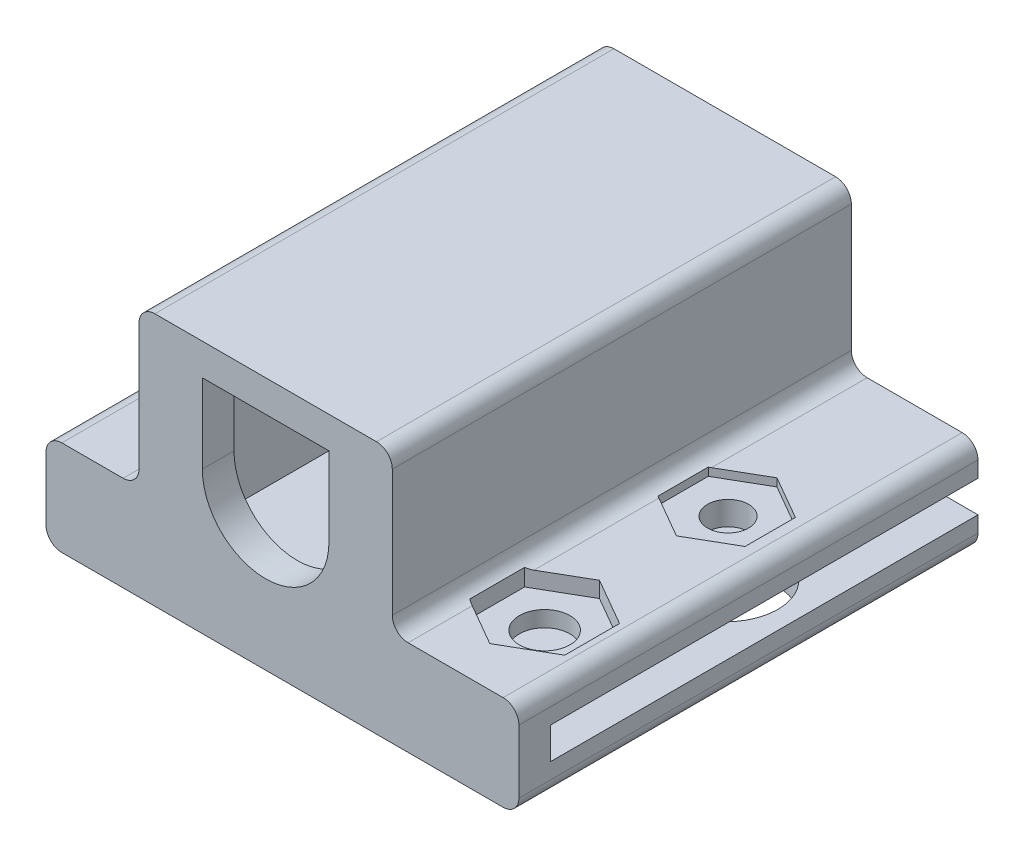
SolidWorks part; units mm, degrees
ref_plane "前视基准面" through (0, 0, 0) normal (0, 0, 1) x (1, 0, 0)
ref_plane "上视基准面" through (0, 0, 0) normal (0, 1, 0) x (1, 0, 0)
ref_plane "右视基准面" through (0, 0, 0) normal (1, 0, 0) x (0, 0, -1)
sketch "草图1" plane through (0, 0, 0) normal (0, 0, 1) x (1, 0, 0)
  line L1 (-12.875, -3) -> (-9, -3)
  line L2 (-13.875, -4) -> (-13.875, -8)
  line L3 (-12.875, -9) -> (15, -9)
  line L4 (5.5, 5) -> (-5.5, 5)
  line L5 (-6, 4.5) -> (-6, -4.5)
  line L6 (-5.5, -5) -> (5.5, -5)
  line L7 (6, -4.5) -> (6, 4.5)
  line L8 (5.5, 5) -> (-5.5, 5)
  line L9 (-6, 4.5) -> (-6, -4.5)
  line L10 (-5.5, -5) -> (5.5, -5)
  line L11 (6, -4.5) -> (6, 4.5)
  line L12 (-11.875, -7) -> (88.125, -7)
  line L13 (88.125, -7) -> (88.125, -5)
  line L14 (88.125, -5) -> (-11.875, -5)
  line L15 (-11.875, -5) -> (-11.875, -7)
  line L16 (-11.875, -7) -> (88.125, -7)
  line L17 (88.125, -7) -> (88.125, -5)
  line L18 (88.125, -5) -> (-11.875, -5)
  line L19 (-11.875, -5) -> (-11.875, -7)
  line L20 (16, -4) -> (16, -8)
  line L21 (-7, 7) -> (7, 7)
  line L22 (-8, 6) -> (-8, -2)
  line L23 (-8, -5) -> (8, -5)
  line L24 (8, 6) -> (8, -2)
  line L25 (9, -3) -> (15, -3)
  line L27 (0.8292, -1.25) -> (0.8292, 1.25)
  line L28 (0.8292, -1.25) -> (0.8292, 1.25)
  line L30 (-4, 0) -> (-4, 5)
  line L31 (-4, 5) -> (4, 5)
  line L32 (4, 0) -> (4, 5)
  arc A0 (-4, 0) -> (4, 0) centre (0, 0) ccw
  arc A1 (0.8292, 1.25) -> (0.8292, -1.25) centre (0, 0) ccw
  arc A2 (0.8292, 1.25) -> (0.8292, -1.25) centre (0, 0) ccw
  arc A3 (-7, 7) -> (-8, 6) centre (-7, 6) ccw
  arc A4 (6, 4.5) -> (5.5, 5) centre (5.5, 4.5) ccw
  arc A5 (-5.5, 5) -> (-6, 4.5) centre (-5.5, 4.5) ccw
  arc A6 (-6, -4.5) -> (-5.5, -5) centre (-5.5, -4.5) ccw
  arc A7 (5.5, -5) -> (6, -4.5) centre (5.5, -4.5) ccw
  arc A8 (6, 4.5) -> (5.5, 5) centre (5.5, 4.5) ccw
  arc A9 (-5.5, 5) -> (-6, 4.5) centre (-5.5, 4.5) ccw
  arc A10 (-6, -4.5) -> (-5.5, -5) centre (-5.5, -4.5) ccw
  arc A11 (5.5, -5) -> (6, -4.5) centre (5.5, -4.5) ccw
  arc A12 (-9, -3) -> (-8, -2) centre (-9, -2) ccw
  arc A13 (-12.875, -3) -> (-13.875, -4) centre (-12.875, -4) ccw
  arc A14 (-12.875, -9) -> (-13.875, -8) centre (-12.875, -8) cw
  arc A15 (15, -9) -> (16, -8) centre (15, -8) ccw
  arc A16 (16, -4) -> (15, -3) centre (15, -4) ccw
  arc A17 (8, -2) -> (9, -3) centre (9, -2) ccw
  arc A18 (8, 6) -> (7, 7) centre (7, 6) ccw
  dimension "D11" = 8
  dimension "D12" = 1
  dimension "D3" = 2
  dimension "D4" = 2
  dimension "D5" = 2
  dimension "D6" = 2
  dimension "D7" = 2
  dimension "D8" = 8
  dimension "D9" = 2
  dimension "D1" = 0
  dimension "D2" = 0
  dimension "D10" = 0
extrude "凸台-拉伸1" add sketch "草图1" along normal blind 2 contours L10 A11 L11 A8 L8 L32 A0 L30 A9 L9 A10 | A11 L18 L20 L25 L24 L21 L22 L1 L2 L3 L16 L19 A10 L9 A9 L8 A8 L11 | L20 L18 L10 L19 L16
sketch "草图2" plane through (0, 0, 0) normal (0, 0, -1) x (-1, 0, 0)
  line L0 (-88.125, -5) -> (11.875, -5) construction
  line L1 (-6, 5) -> (6, 5)
  line L2 (-6, 5) -> (-6, -5)
  line L4 (-6, 4.5) -> (-6, -4.5)
  line L5 (-5.5, -5) -> (5.5, -5)
  line L6 (6, -4.5) -> (6, 4.5)
  line L7 (5.5, 5) -> (-5.5, 5)
  line L8 (-16, -4) -> (-16, -8)
  line L9 (-15, -9) -> (12.875, -9)
  line L10 (13.875, -8) -> (13.875, -4)
  line L11 (12.875, -3) -> (9, -3)
  line L12 (8, -2) -> (8, 6)
  line L13 (7, 7) -> (-7, 7)
  line L14 (-8, 6) -> (-8, -2)
  line L15 (-9, -3) -> (-15, -3)
  line L16 (-16, -4) -> (-16, -8)
  line L17 (-15, -9) -> (12.875, -9)
  line L18 (13.875, -8) -> (13.875, -4)
  line L19 (12.875, -3) -> (9, -3)
  line L20 (8, -2) -> (8, 6)
  line L21 (7, 7) -> (-7, 7)
  line L22 (-8, 6) -> (-8, -2)
  line L23 (-9, -3) -> (-15, -3)
  line L24 (-6, 4.5) -> (-6, -4.5)
  line L26 (6, -4.5) -> (6, 4.5)
  line L27 (5.5, 5) -> (-5.5, 5)
  line L28 (6, 5) -> (6, -5)
  line L33 (-6, -5) -> (-88.125, -5)
  line L37 (-88.125, -7) -> (11.875, -7)
  line L38 (-88.125, -5) -> (-88.125, -7)
  line L39 (11.875, -5) -> (-88.125, -5)
  line L40 (11.875, -7) -> (11.875, -5)
  line L41 (-88.125, -7) -> (11.875, -7)
  line L42 (-88.125, -5) -> (-88.125, -7)
  line L43 (11.875, -5) -> (6, -5)
  line L44 (11.875, -7) -> (11.875, -5)
  arc A4 (-5.5, 5) -> (-6, 4.5) centre (-5.5, 4.5) ccw
  arc A5 (-6, -4.5) -> (-5.5, -5) centre (-5.5, -4.5) ccw
  arc A6 (5.5, -5) -> (6, -4.5) centre (5.5, -4.5) ccw
  arc A7 (6, 4.5) -> (5.5, 5) centre (5.5, 4.5) ccw
  arc A8 (-5.5, 5) -> (-6, 4.5) centre (-5.5, 4.5) ccw
  arc A11 (6, 4.5) -> (5.5, 5) centre (5.5, 4.5) ccw
  arc A16 (-16, -8) -> (-15, -9) centre (-15, -8) ccw
  arc A17 (-16, -8) -> (-15, -9) centre (-15, -8) ccw
  arc A18 (12.875, -9) -> (13.875, -8) centre (12.875, -8) ccw
  arc A19 (12.875, -9) -> (13.875, -8) centre (12.875, -8) ccw
  arc A20 (13.875, -4) -> (12.875, -3) centre (12.875, -4) ccw
  arc A21 (13.875, -4) -> (12.875, -3) centre (12.875, -4) ccw
  arc A22 (8, -2) -> (9, -3) centre (9, -2) ccw
  arc A23 (8, -2) -> (9, -3) centre (9, -2) ccw
  arc A24 (8, 6) -> (7, 7) centre (7, 6) ccw
  arc A25 (8, 6) -> (7, 7) centre (7, 6) ccw
  arc A26 (-7, 7) -> (-8, 6) centre (-7, 6) ccw
  arc A27 (-7, 7) -> (-8, 6) centre (-7, 6) ccw
  arc A28 (-9, -3) -> (-8, -2) centre (-9, -2) ccw
  arc A29 (-9, -3) -> (-8, -2) centre (-9, -2) ccw
  arc A30 (-15, -3) -> (-16, -4) centre (-15, -4) ccw
  arc A31 (-15, -3) -> (-16, -4) centre (-15, -4) ccw
  point P26 (6, 0)
  line M20 (-16, -4) -> (-16, -8)
  line M21 (-15, -9) -> (12.875, -9)
  line M22 (13.875, -8) -> (13.875, -4)
  line M23 (12.875, -3) -> (9, -3)
  line M24 (8, -2) -> (8, 6)
  line M25 (7, 7) -> (-7, 7)
  line M26 (-8, 6) -> (-8, -2)
  line M27 (-9, -3) -> (-15, -3)
  line M28 (-4, 5) -> (4, 5)
  dimension "D3" = 0
  dimension "D4" = 0
  dimension "D5" = 0
  dimension "D1" = 0
  dimension "D2" = 0
extrude "凸台-拉伸2" add sketch "草图2" along normal offset from surface (27 mm away) 2 contours L44 L41 L16 L43 L2 L1 L28 L26 M21 M22 M23 M24 M25 M26 M27 M20 M28
sketch "草图4" plane through (0, -9, 0) normal (0, -1, 0) x (1, 0, 0)
  line L0 (9.33, -14.175) -> (13.92, -16.825) construction
  line L2 (11.625, -18.7274) -> (14.42, -17.1137)
  line L3 (14.42, -17.1137) -> (14.42, -13.8863)
  line L4 (-12.875, 2) -> (-12.875, -27)
  line L5 (-12.875, -27) -> (15, -27)
  line L6 (-12.875, 2) -> (-12.875, -27)
  line L7 (15, 2) -> (-12.875, 2)
  line L11 (15, 2) -> (-12.875, 2)
  line L12 (14.42, -13.8863) -> (11.625, -12.2726)
  line L13 (11.625, -12.2726) -> (8.83, -13.8863)
  line L14 (9.33, -14.175) -> (9.33, -16.825)
  line L15 (9.33, -16.825) -> (11.625, -18.15)
  line L16 (11.625, -18.15) -> (13.92, -16.825)
  line L17 (13.92, -16.825) -> (13.92, -14.175)
  line L18 (13.92, -14.175) -> (11.625, -12.85)
  line L19 (11.625, -12.85) -> (9.33, -14.175)
  line L20 (9.33, -14.175) -> (9.33, -16.825)
  line L21 (9.33, -16.825) -> (11.625, -18.15)
  line L22 (11.625, -18.15) -> (13.92, -16.825)
  line L23 (13.92, -16.825) -> (13.92, -14.175)
  line L24 (13.92, -14.175) -> (11.625, -12.85)
  line L25 (11.625, -12.85) -> (9.33, -14.175)
  line L26 (8.83, -13.8863) -> (8.83, -17.1137)
  line L27 (8.83, -17.1137) -> (11.625, -18.7274)
  line L31 (-12.875, -27) -> (15, -27)
  line L32 (15, -27) -> (15, 2)
  line L33 (15, -27) -> (15, 2)
  circle A0 centre (11.625, -15.5) radius 2.795 construction
  circle A1 centre (11.625, -15.5) radius 3.2274
  dimension "D3" = 0.5
  dimension "D1" = 0
  dimension "D2" = 0
extrude "切除-拉伸1" cut sketch "草图4" against normal blind 2 contours A1
sketch "草图5" plane through (0, -3, 0) normal (0, 1, 0) x (1, 0, 0)
  line L1 (11.625, 18.6754) -> (8.875, 17.0877)
  line L2 (8.875, 17.0877) -> (8.875, 13.9123)
  line L3 (8.875, 13.9123) -> (11.625, 12.3246)
  line L4 (15, -2) -> (15, 27)
  line L5 (15, 27) -> (9, 27)
  line L6 (15, -2) -> (15, 27)
  line L7 (9, -2) -> (15, -2)
  line L11 (9, -2) -> (15, -2)
  line L12 (11.625, 12.3246) -> (14.375, 13.9123)
  line L13 (14.375, 13.9123) -> (14.375, 17.0877)
  line L14 (14.375, 17.0877) -> (11.625, 18.6754)
  line L18 (15, 27) -> (9, 27)
  line L19 (9, 27) -> (9, -2)
  line L20 (9, 27) -> (9, -2)
  circle A0 centre (11.625, 15.5) radius 3
  circle A1 centre (11.625, 15.5) radius 1.25
  circle A2 centre (11.625, 15.5) radius 1.25
  circle A3 centre (11.625, 15.5) radius 2.75 construction
  dimension "D3" = 5.5
  dimension "D1" = 0
  dimension "D2" = 0
extrude "切除-拉伸2" cut sketch "草图5" against normal blind 0.5 and the other way through all contours L12 L13 L14 L1 L2 L3
sketch "草图6" plane through (0, -3, 0) normal (0, 1, 0) x (1, 0, 0)
  line L0 (11.625, 18.6754) -> (11.625, -2) construction
  line L2 (14.625, 2.2679) -> (14.625, 5.7321)
  line L3 (14.625, 5.7321) -> (11.625, 7.4641)
  line L4 (11.625, 12.3246) -> (9, 13.8401)
  line L5 (15, 27) -> (9, 27)
  line L6 (11.625, 12.3246) -> (9, 13.8401)
  line L7 (9, -2) -> (15, -2)
  line L11 (9, -2) -> (15, -2)
  line L12 (11.625, 7.4641) -> (8.625, 5.7321)
  line L13 (8.625, 5.7321) -> (8.625, 2.2679)
  line L14 (14.375, 13.9123) -> (14.375, 17.0877)
  line L15 (14.375, 17.0877) -> (11.625, 18.6754)
  line L16 (11.625, 18.6754) -> (8.875, 17.0877)
  line L17 (8.875, 17.0877) -> (8.875, 13.9123)
  line L18 (8.875, 13.9123) -> (11.625, 12.3246)
  line L19 (11.625, 12.3246) -> (14.375, 13.9123)
  line L20 (14.375, 13.9123) -> (14.375, 17.0877)
  line L21 (14.375, 17.0877) -> (11.625, 18.6754)
  line L22 (11.625, 18.6754) -> (8.875, 17.0877)
  line L23 (8.875, 17.0877) -> (8.875, 13.9123)
  line L24 (8.875, 13.9123) -> (11.625, 12.3246)
  line L25 (11.625, 12.3246) -> (14.375, 13.9123)
  line L26 (8.625, 2.2679) -> (11.625, 0.5359)
  line L27 (11.625, 0.5359) -> (14.625, 2.2679)
  line L31 (15, 27) -> (9, 27)
  line L38 (9, 13.8401) -> (9, -2)
  line L39 (9, 13.8401) -> (9, -2)
  line L40 (15, -2) -> (15, 27)
  line L41 (15, -2) -> (15, 27)
  line L42 (9, 27) -> (9, 17.1599)
  line L43 (9, 27) -> (9, 17.1599)
  line L44 (9, 17.1599) -> (11.625, 18.6754)
  line L45 (9, 17.1599) -> (11.625, 18.6754)
  line L46 (11.625, 18.6754) -> (14.375, 17.0877)
  line L47 (11.625, 18.6754) -> (14.375, 17.0877)
  line L48 (14.375, 17.0877) -> (14.375, 13.9123)
  line L49 (14.375, 17.0877) -> (14.375, 13.9123)
  line L50 (14.375, 13.9123) -> (11.625, 12.3246)
  line L51 (14.375, 13.9123) -> (11.625, 12.3246)
  circle A0 centre (11.625, 4) radius 3 construction
  dimension "D3" = 6
  dimension "D4" = 6
  dimension "D1" = 0
  dimension "D2" = 0
extrude "切除-拉伸3" cut sketch "草图6" against normal blind 1 and the other way through all contours L12 L13 L26 L27 L2 L3
sketch "草图8" plane through (0, 0, -27) normal (0, 0, -1) x (-1, 0, 0)
  line L0 (6, -5) -> (6, 5) construction
  line L1 (-6, 5) -> (6, 5)
  line L2 (-6, 5) -> (-6, 4)
  line L3 (-6, 4) -> (6, 4)
  line L4 (6, 5) -> (6, 4)
  dimension "D1" = 1
extrude "凸台-拉伸3" add sketch "草图8" against normal blind 1.6
sketch "草图10" plane through (0, -4, 0) normal (0, 1, 0) x (1, 0, 0)
  line L0 (11.625, 0.5359) -> (11.625, 7.4641) construction
  line L6 (14.625, 5.7321) -> (11.625, 7.4641)
  line L7 (11.625, 7.4641) -> (8.625, 5.7321)
  line L8 (8.625, 5.7321) -> (8.625, 2.2679)
  line L9 (8.625, 2.2679) -> (11.625, 0.5359)
  line L10 (11.625, 0.5359) -> (14.625, 2.2679)
  line L11 (14.625, 2.2679) -> (14.625, 5.7321)
  line L12 (14.625, 5.7321) -> (11.625, 7.4641)
  line L13 (11.625, 7.4641) -> (8.625, 5.7321)
  line L14 (8.625, 5.7321) -> (8.625, 2.2679)
  line L15 (8.625, 2.2679) -> (11.625, 0.5359)
  line L16 (11.625, 0.5359) -> (14.625, 2.2679)
  line L17 (14.625, 2.2679) -> (14.625, 5.7321)
  circle A0 centre (11.625, 4) radius 1.6
  dimension "D2" = 3.2
  dimension "D1" = 0
extrude "切除-拉伸4" cut sketch "草图10" against normal through all contours A0
sketch "草图11" plane through (0, -3.5, 0) normal (0, 1, 0) x (1, 0, 0)
  line L0 (11.7325, 12.3866) -> (11.625, 18.6754) construction
  line L6 (8.875, 13.9123) -> (11.625, 12.3246)
  line L7 (11.625, 12.3246) -> (14.375, 13.9123)
  line L8 (14.375, 13.9123) -> (14.375, 17.0877)
  line L9 (14.375, 17.0877) -> (11.625, 18.6754)
  line L10 (11.625, 18.6754) -> (8.875, 17.0877)
  line L11 (8.875, 17.0877) -> (8.875, 13.9123)
  line L12 (8.875, 13.9123) -> (11.625, 12.3246)
  line L13 (11.625, 12.3246) -> (14.375, 13.9123)
  line L14 (14.375, 13.9123) -> (14.375, 17.0877)
  line L15 (14.375, 17.0877) -> (11.625, 18.6754)
  line L16 (11.625, 18.6754) -> (8.875, 17.0877)
  line L17 (8.875, 17.0877) -> (8.875, 13.9123)
  circle A0 centre (11.6788, 15.531) radius 1.3
  dimension "D2" = 2.6
  dimension "D1" = 0
extrude "切除-拉伸5" cut sketch "草图11" against normal through all contours A0
